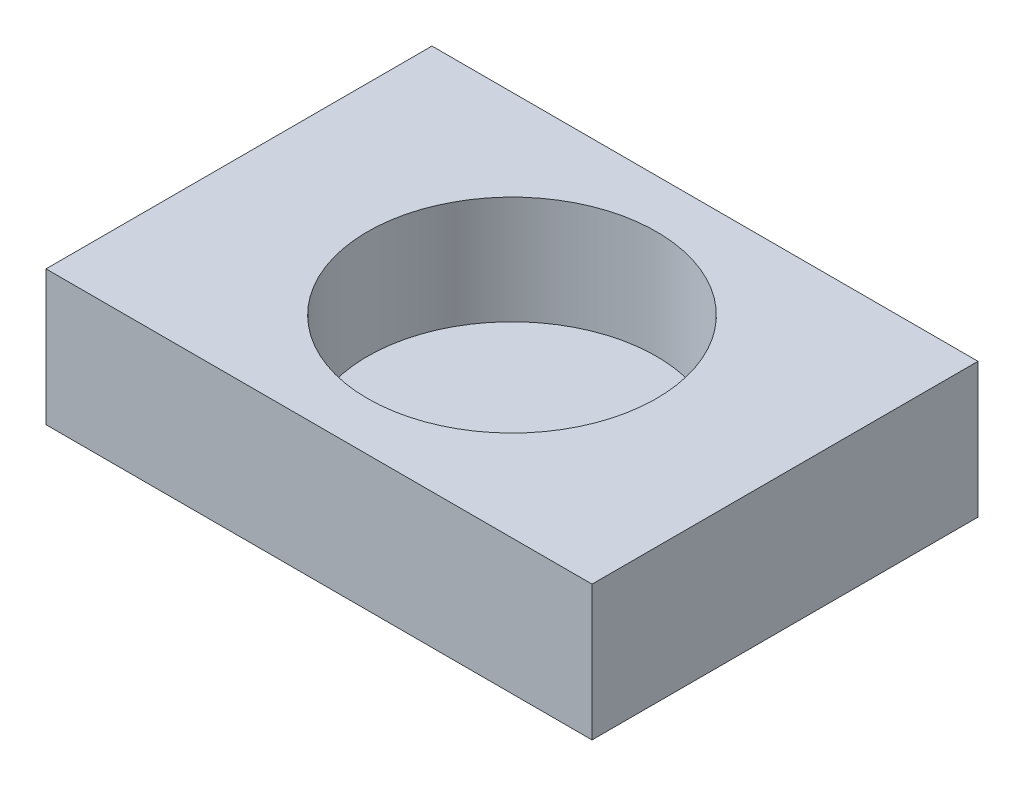
SolidWorks part; units mm, degrees
ref_plane "Front Plane" through (0, 0, 0) normal (0, 0, 1) x (1, 0, 0)
ref_plane "Top Plane" through (0, 0, 0) normal (0, 1, 0) x (1, 0, 0)
ref_plane "Right Plane" through (0, 0, 0) normal (1, 0, 0) x (0, 0, -1)
sketch "Sketch2" plane through (0, 0, 0) normal (0, 1, 0) x (1, 0, 0)
  line L0 (0, 71.4945) -> (0, -71.4945) construction
  line L1 (101.1455, 71.4945) -> (-101.1455, 71.4945)
  line L2 (101.1455, 71.4945) -> (101.1455, -71.4945)
  line L3 (101.1455, -71.4945) -> (-101.1455, -71.4945)
  line L4 (-101.1455, 71.4945) -> (-101.1455, -71.4945)
  point P6 (0, 0)
  point P7 (0, 71.4945)
  dimension "D2" = 202.2911
  dimension "D1" = 142.989
extrude "Boss-Extrude2" add sketch "Sketch2" along normal blind 50
sketch "Sketch3" plane through (0, 50, -33.6977) normal (0, 1, 0) x (1, 0, 0)
  line L0 (0, 37.7968) -> (0, -105.1922) construction
  line L1 (101.1455, 37.7968) -> (-101.1455, 37.7968) construction
  line L2 (-101.1455, -105.1922) -> (101.1455, -105.1922) construction
  circle A0 centre (0, -33.6977) radius 53.5401
  point P2 (0, -33.6977)
  dimension "D1" = 107.0802
extrude "Cut-Extrude2" cut sketch "Sketch3" against normal blind 40
ref_point "Point3"
ref_plane "Plane1" through (0, 60, 0) normal (0, 1, 0) x (1, 0, 0)
